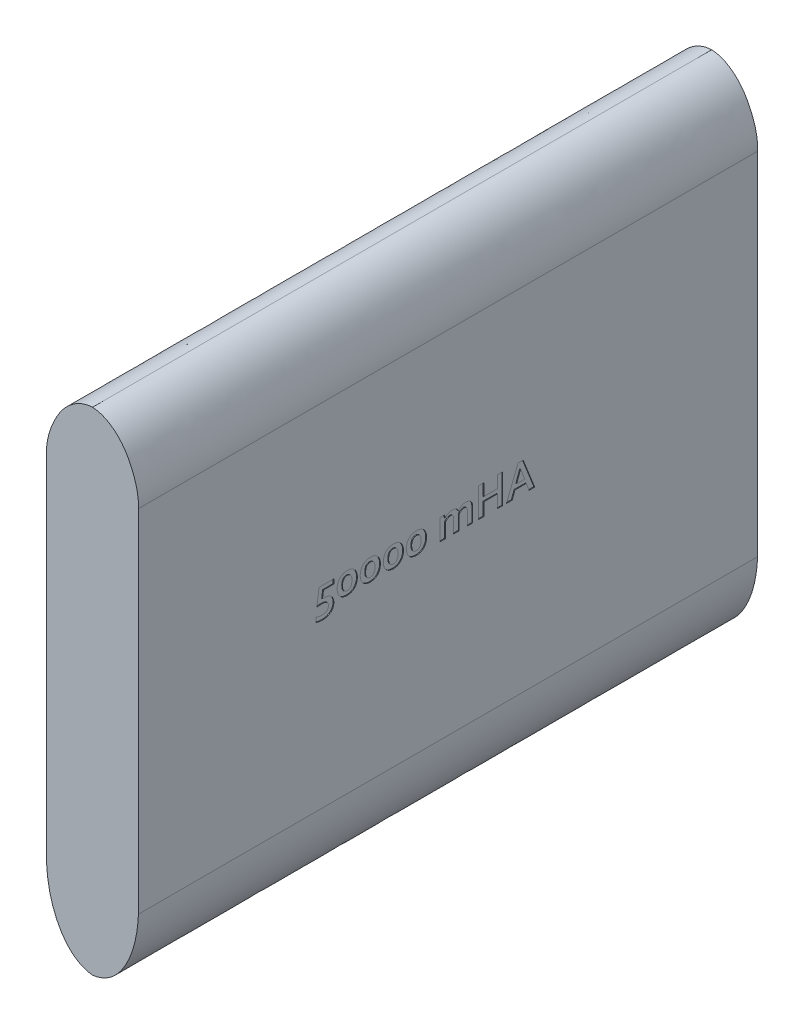
SolidWorks part; units mm, degrees
material "Plastique personnalisé"
ref_plane "Plan de face" through (0, 0, 0) normal (0, 0, 1) x (1, 0, 0)
ref_plane "Plan de dessus" through (0, 0, 0) normal (0, 1, 0) x (1, 0, 0)
ref_plane "Plan de droite" through (0, 0, 0) normal (1, 0, 0) x (0, 0, -1)
sketch "Esquisse1" plane through (0, 0, 0) normal (0, 0, 1) x (1, 0, 0)
  line L0 (174.3639, 770.1527) -> (203.7631, 769.9415) construction
  line L1 (174.0061, 829.7417) -> (203.7153, 829.7417) construction
  line L2 (203.7153, 716.3188) -> (174.0061, 716.3188) construction
  line L3 (188.8607, 716.3188) -> (188.8607, 829.7417) construction
  line L4 (188.8607, 829.7417) -> (188.8607, 850.6872) construction
  line L5 (188.8607, 716.3188) -> (188.8607, 691.8413) construction
  line L6 (174.0061, 716.3188) -> (174.0061, 829.7417)
  line L7 (203.7153, 829.7417) -> (203.7153, 716.3188)
  spline S0 degree 3 poles (174.0061, 829.7417) (173.8251, 833.5473) (175.4076, 839.0771) (180.026, 847.0966) (185.1378, 850.6021) (188.8607, 850.6872) knots 0 0 0 0 0.407149 0.601732 1 1 1 1
  spline S1 degree 3 poles (203.7153, 829.7417) (203.8963, 833.5473) (202.3138, 839.0771) (197.6954, 847.0966) (192.5836, 850.6021) (188.8607, 850.6872) knots 0 0 0 0 0.407149 0.601732 1 1 1 1
  spline S2 degree 3 poles (174.0061, 716.3188) (174.23, 711.367) (176.075, 701.1756) (183.136, 692.4997) (188.8607, 691.8413) knots 0 0 0 0 0.482436 1 1 1 1
  spline S3 degree 3 poles (203.7153, 716.3188) (203.4913, 711.367) (201.6464, 701.1756) (194.5854, 692.4997) (188.8607, 691.8413) knots 0 0 0 0 0.482436 1 1 1 1
  dimension "D1" = 29.4
extrude "Boss.-Extru.1" add sketch "Esquisse1" along normal blind 200
sketch "Esquisse3" plane through (203.7153, 0, 0) normal (1, 0, 0) x (0, 0, -1)
  text T0 "<b>50000 mHA</b>" font "Corbel" height in points 36
extrude "Enlèv. mat.-Extru.1" cut sketch "Esquisse3" against normal blind 0.25
